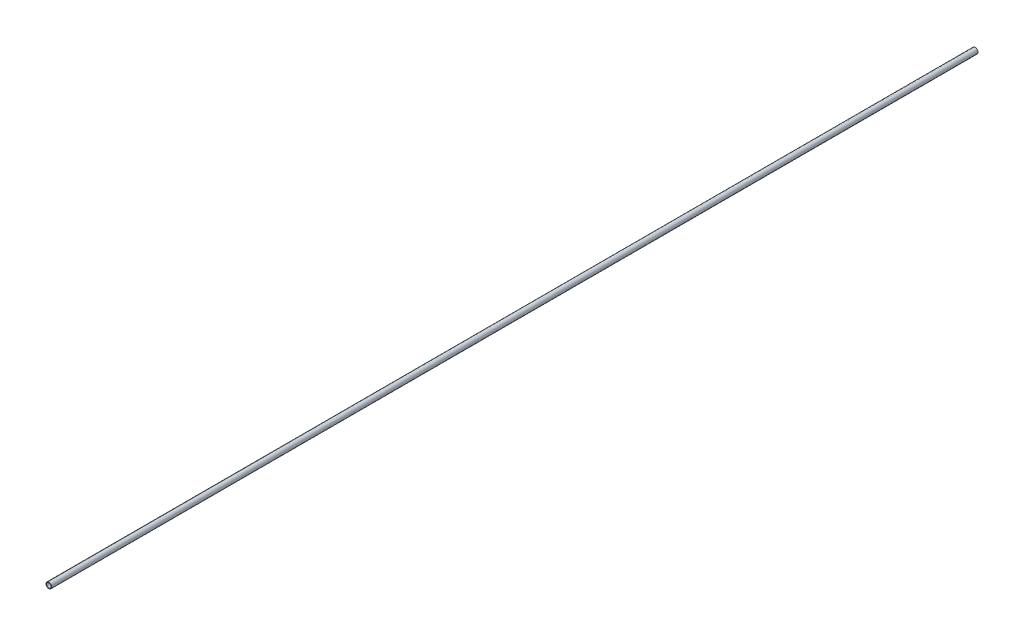
SolidWorks part; units mm, degrees
ref_plane "Front" through (0, 0, 0) normal (0, 0, 1) x (1, 0, 0)
ref_plane "Top" through (0, 0, 0) normal (0, 1, 0) x (1, 0, 0)
ref_plane "Side" through (0, 0, 0) normal (1, 0, 0) x (0, 0, -1)
sketch "PipeSketch" plane through (0, 0, 0) normal (0, 0, 1) x (1, 0, 0)
  circle A0 centre (0, 0) radius 16.764
  circle A1 centre (0, 0) radius 13.3858
  dimension "OuterDiameter" = 33.528
  dimension "InnerDiameter" = 26.7716
extrude "Extrusion" add sketch "PipeSketch" along normal blind 5486.4
sketch "FilterSketch" plane through (0, 0, 0) normal (0, 0, 1) x (1, 0, 0)
  circle A0 centre (0, 0) radius 12.7 construction
  dimension "NominalDiameter" = 25.4
